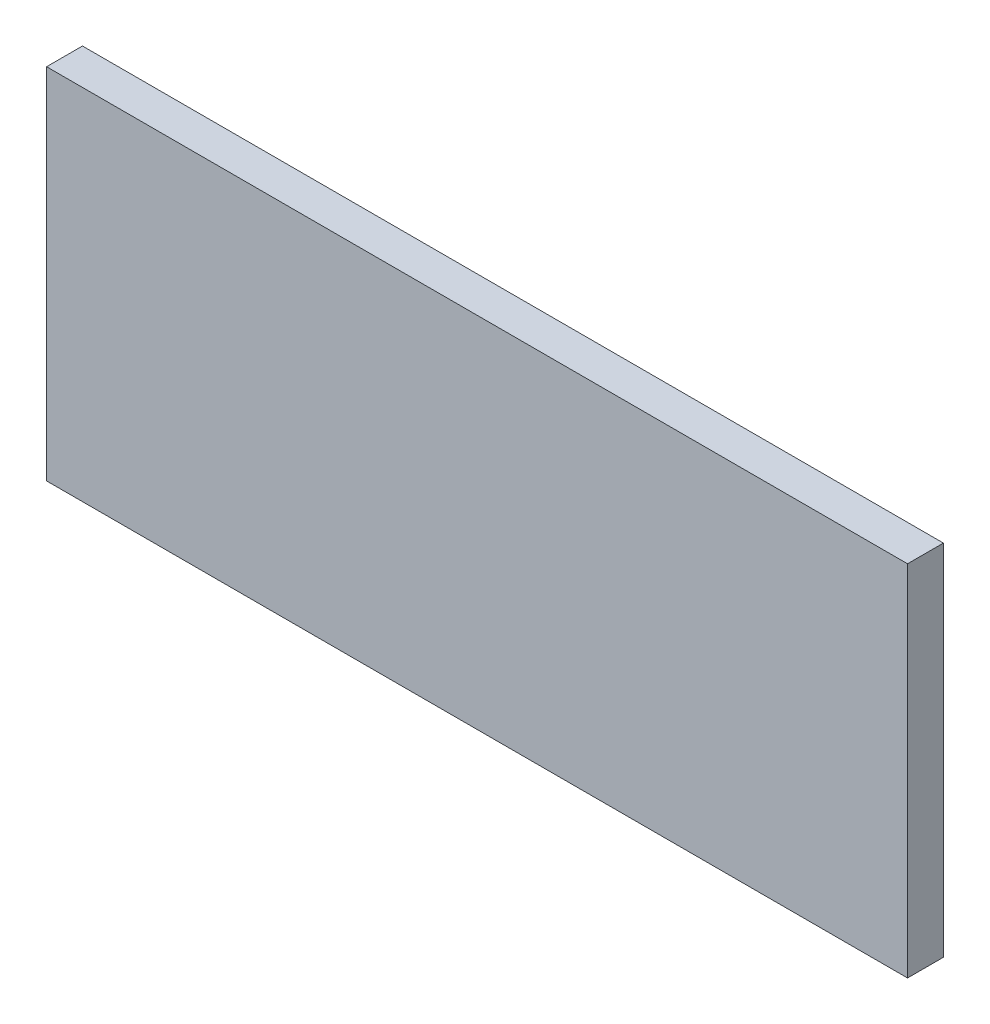
SolidWorks part; units mm, degrees
ref_plane "Front Plane" through (0, 0, 0) normal (0, 0, 1) x (1, 0, 0)
ref_plane "Top Plane" through (0, 0, 0) normal (0, 1, 0) x (1, 0, 0)
ref_plane "Right Plane" through (0, 0, 0) normal (1, 0, 0) x (0, 0, -1)
sketch "Sketch1" plane through (0, 0, 0) normal (0, 0, 1) x (1, 0, 0)
  line L1 (0, 0) -> (304.8, 0)
  line L2 (0, 0) -> (0, -127)
  line L3 (0, -127) -> (304.8, -127)
  line L4 (304.8, 0) -> (304.8, -127)
  dimension "D1" = 304.8
  dimension "D2" = 127
extrude "Boss-Extrude1" add sketch "Sketch1" along normal blind 12.7
